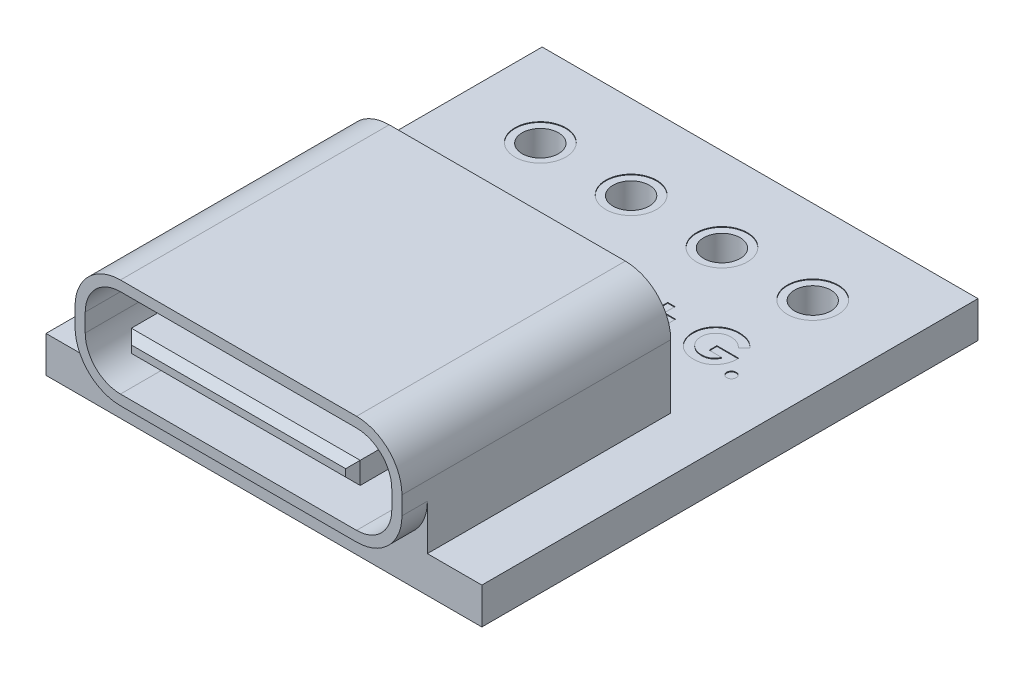
SolidWorks part; units mm, degrees
ref_plane "Front Plane" through (0, 0, 0) normal (0, 0, 1) x (1, 0, 0)
ref_plane "Top Plane" through (0, 0, 0) normal (0, 1, 0) x (1, 0, 0)
ref_plane "Right Plane" through (0, 0, 0) normal (1, 0, 0) x (0, 0, -1)
sketch "Sketch2" plane through (0, 0, 0) normal (0, 1, 0) x (1, 0, 0)
  line L1 (6, -6.83) -> (-6, -6.83)
  line L2 (6, -6.83) -> (6, 6.83)
  line L3 (6, 6.83) -> (-6, 6.83)
  line L4 (-6, -6.83) -> (-6, 6.83)
  line L5 (6, -6.83) -> (-6, 6.83) construction
  line L6 (6, 6.83) -> (-6, -6.83) construction
  point P0 (0, 0)
  dimension "D1" = 12
  dimension "D2" = 13.66
extrude "Boss-Extrude2" add sketch "Sketch2" along normal blind 1
ref_plane "Plane1" through (0, 0, 7.53) normal (0, 0, 1) x (1, 0, 0)
sketch "Sketch3" plane through (0, 0, 7.53) normal (0, 0, 1) x (1, 0, 0)
  line L0 (-6, 1) -> (6, 1) construction
  line L1 (4.5, 4) -> (-4.5, 4)
  line L2 (4.5, 4) -> (4.5, 1)
  line L3 (4.5, 1) -> (-4.5, 1)
  line L4 (-4.5, 4) -> (-4.5, 1)
  line L5 (4.5, 4) -> (-4.5, 1) construction
  line L6 (4.5, 1) -> (-4.5, 4) construction
  point P0 (0, 2.5)
  dimension "D1" = 3
  dimension "D2" = 9
extrude "Boss-Extrude3" add sketch "Sketch3" against normal blind 7.4
fillet "Fillet1" radius 1.25 4 edges at (-4.5, 1, 7.18) (4.5, 1, 7.18) (-4.5, 4, 3.83) (4.5, 4, 3.83)
sketch "Sketch4" plane through (0, 0, 7.53) normal (0, 0, 1) x (1, 0, 0)
  line L4 (-4.5, 2.75) -> (-4.5, 2.25) construction
  line L5 (3.15, 2.2) -> (-3.15, 2.2)
  line L6 (3.15, 2.2) -> (3.15, 2.8)
  line L7 (3.15, 2.8) -> (-3.15, 2.8)
  line L8 (-4.22, 2.75) -> (-4.22, 2.25)
  line L9 (-3.25, 1.28) -> (3.25, 1.28)
  line L10 (4.22, 2.25) -> (4.22, 2.75)
  line L11 (3.25, 3.72) -> (-3.25, 3.72)
  line L12 (-4.22, 2.75) -> (-4.22, 2.25)
  line L13 (-3.25, 1.28) -> (3.25, 1.28)
  line L14 (4.22, 2.25) -> (4.22, 2.75)
  line L15 (3.25, 3.72) -> (-3.25, 3.72)
  line L16 (-3.15, 2.2) -> (-3.15, 2.8)
  line L17 (3.15, 2.2) -> (-3.15, 2.8) construction
  line L18 (3.15, 2.8) -> (-3.15, 2.2) construction
  arc A8 (-4.22, 2.25) -> (-3.25, 1.28) centre (-3.25, 2.25) ccw
  arc A9 (3.25, 1.28) -> (4.22, 2.25) centre (3.25, 2.25) ccw
  arc A10 (4.22, 2.75) -> (3.25, 3.72) centre (3.25, 2.75) ccw
  arc A11 (-3.25, 3.72) -> (-4.22, 2.75) centre (-3.25, 2.75) ccw
  arc A12 (-4.22, 2.25) -> (-3.25, 1.28) centre (-3.25, 2.25) ccw
  arc A13 (3.25, 1.28) -> (4.22, 2.25) centre (3.25, 2.25) ccw
  arc A14 (4.22, 2.75) -> (3.25, 3.72) centre (3.25, 2.75) ccw
  arc A15 (-3.25, 3.72) -> (-4.22, 2.75) centre (-3.25, 2.75) ccw
  point P0 (0, 2.5)
  point P9 (-4.5, 2.5)
  dimension "D2" = 0
  dimension "D3" = 0.6
  dimension "D4" = 6.3
  dimension "D1" = 0.28
extrude "Cut-Extrude1" cut sketch "Sketch4" against normal offset from surface (5.4 mm away) 2 up to face at (0, 2.6696, 0.13)
chamfer "Chamfer1" distance 0.2 angle 45 4 edges at (-3.15, 2.5, 7.53) (0, 2.2, 7.53) (3.15, 2.5, 7.53) (0, 2.8, 7.53)
sketch "Sketch5" plane through (0, 1, 0) normal (0, 1, 0) x (1, 0, 0)
  line L0 (-3.75, 4.53) -> (3.75, 4.53) construction
  line L1 (6, 6.83) -> (-6, 6.83) construction
  circle A0 centre (-3.75, 4.53) radius 0.5
  circle A1 centre (-1.25, 4.53) radius 0.5
  circle A2 centre (1.25, 4.53) radius 0.5
  circle A3 centre (3.75, 4.53) radius 0.5
  point P11 (0, 4.53)
  dimension "D4" = 1
  dimension "D1" = 0
  dimension "D2" = 2.3
  dimension "D3" = 7.5
extrude "Cut-Extrude2" cut sketch "Sketch5" against normal through all
sketch "Sketch6" plane through (0, 1, 0) normal (0, 1, 0) x (1, 0, 0)
  circle A33 centre (-3.75, 4.53) radius 0.7
  circle A34 centre (-3.75, 4.53) radius 0.7
  circle A36 centre (-1.25, 4.53) radius 0.7
  circle A37 centre (-1.25, 4.53) radius 0.7
  circle A39 centre (1.25, 4.53) radius 0.7
  circle A40 centre (1.25, 4.53) radius 0.7
  circle A42 centre (3.75, 4.53) radius 0.7
  circle A43 centre (3.75, 4.53) radius 0.7
extrude "Cut-Extrude3" cut sketch "Sketch6" against normal blind 0.02
sketch "Sketch7" plane through (0, 0, 0) normal (0, -1, 0) x (1, 0, 0)
  circle A2 centre (-3.75, -4.53) radius 0.7
  circle A3 centre (-3.75, -4.53) radius 0.7
  circle A5 centre (-1.25, -4.53) radius 0.7
  circle A6 centre (-1.25, -4.53) radius 0.7
  circle A8 centre (1.25, -4.53) radius 0.7
  circle A9 centre (1.25, -4.53) radius 0.7
  circle A11 centre (3.75, -4.53) radius 0.7
  circle A12 centre (3.75, -4.53) radius 0.7
extrude "Cut-Extrude4" cut sketch "Sketch7" against normal blind 0.02
sketch "Sketch8" plane through (0, 1, 0) normal (0, 1, 0) x (1, 0, 0)
  line L0 (-4.75, 1.5) -> (-2.75, 1.5) construction
  line L1 (-2.25, 1.5) -> (-0.25, 1.5) construction
  line L2 (0.25, 1.5) -> (2.25, 1.5) construction
  line L3 (2.75, 1.5) -> (4.75, 1.5) construction
  circle A0 centre (3.75, 4.53) radius 0.5 construction
  circle A3 centre (-3.75, 4.53) radius 0.5 construction
  circle A4 centre (-1.25, 4.53) radius 0.5 construction
  circle A5 centre (1.25, 4.53) radius 0.5 construction
  text T0 "<b>V</b>" font "Century Gothic" height 1.2
  text T1 "<b>D-</b>" font "Century Gothic" height 1.2
  text T2 "<b>D+</b>" font "Century Gothic" height 1.2
  text T3 "<b>G.</b>" font "Century Gothic" height 1.2
  point P2 (3.75, 1.5)
  point P12 (-1.25, 1.5)
  point P14 (-3.75, 1.5)
  point P18 (1.25, 1.5)
  dimension "D1" = 0
  dimension "D2" = 1.5
  dimension "D3" = 0
  dimension "D4" = 0
  dimension "D5" = 2
  dimension "D6" = 0
extrude "Cut-Extrude5" cut sketch "Sketch8" against normal blind 0.02
